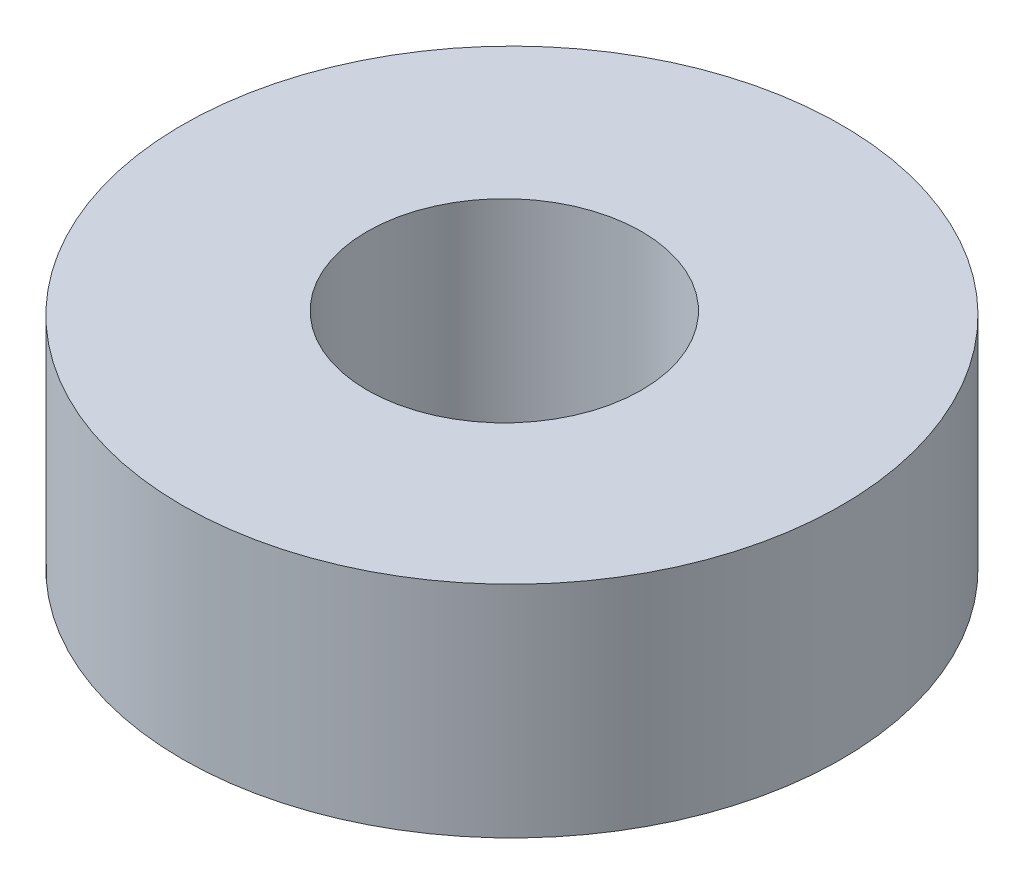
SolidWorks part; units mm, degrees
material "Cast Alloy Steel"
ref_plane "Front Plane" through (0, 0, 0) normal (0, 0, 1) x (1, 0, 0)
ref_plane "Top Plane" through (0, 0, 0) normal (0, 1, 0) x (1, 0, 0)
ref_plane "Right Plane" through (0, 0, 0) normal (1, 0, 0) x (0, 0, -1)
sketch "Sketch1" plane through (0, 0, 0) normal (0, 1, 0) x (1, 0, 0)
  circle A0 centre (0, 0) radius 2.5
  circle A1 centre (0.1386, 0) radius 6
extrude "Boss-Extrude1" add sketch "Sketch1" along normal blind 4
